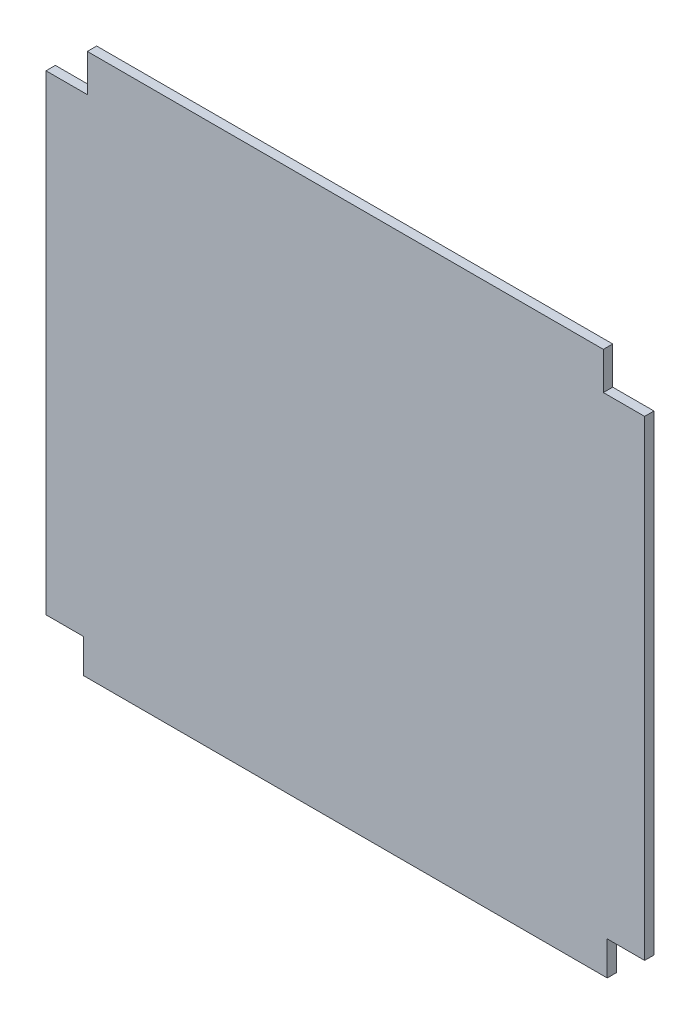
SolidWorks part; units mm, degrees
ref_plane "Plan de face" through (0, 0, 0) normal (0, 0, 1) x (1, 0, 0)
ref_plane "Plan de dessus" through (0, 0, 0) normal (0, 1, 0) x (1, 0, 0)
ref_plane "Plan de droite" through (0, 0, 0) normal (1, 0, 0) x (0, 0, -1)
sketch "Esquisse1" plane through (0, 0, 0) normal (0, 0, 1) x (1, 0, 0)
  line L1 (-280, -290) -> (280, -290)
  line L2 (-320, -253.75) -> (-320, 250)
  line L3 (-275.8621, 290) -> (275.8621, 290)
  line L4 (320, -253.75) -> (320, 250)
  line L5 (-280, -253.75) -> (275.8621, 250) construction
  line L6 (-275.8621, 250) -> (280, -253.75) construction
  line L9 (320, -253.75) -> (280, -253.75)
  line L10 (280, -290) -> (280, -253.75)
  line L13 (-320, -253.75) -> (-280, -253.75)
  line L14 (-280, -290) -> (-280, -253.75)
  line L17 (320, 250) -> (275.8621, 250)
  line L18 (275.8621, 290) -> (275.8621, 250)
  line L21 (-320, 250) -> (-275.8621, 250)
  line L22 (-275.8621, 290) -> (-275.8621, 250)
  point P0 (0, 0)
  dimension "D3" = 40
  dimension "D4" = 40
  dimension "D5" = 40
  dimension "D6" = 40
extrude "Boss.-Extru.2" add sketch "Esquisse1" along normal blind 10
